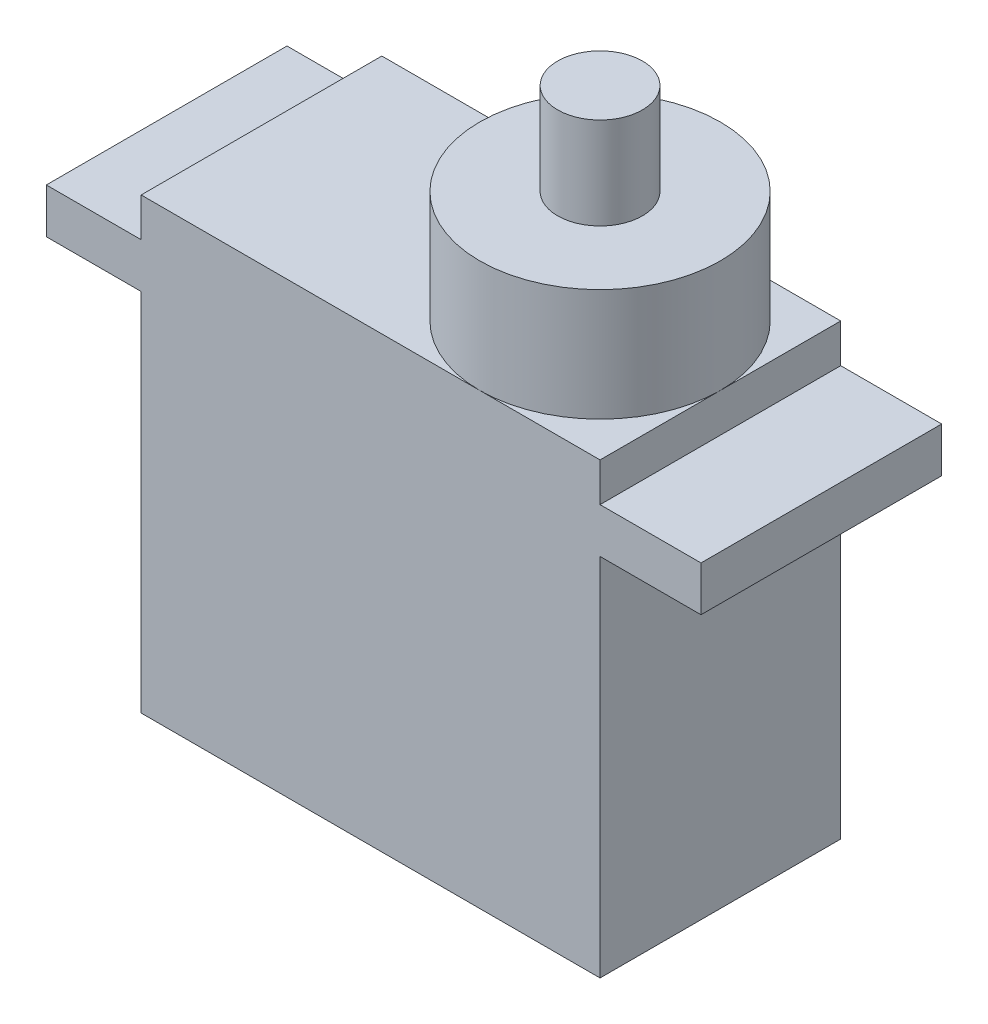
SolidWorks part; units mm, degrees
material "PF"
ref_plane "Front Plane" through (0, 0, 0) normal (0, 0, 1) x (1, 0, 0)
ref_plane "Top Plane" through (0, 0, 0) normal (0, 1, 0) x (1, 0, 0)
ref_plane "Right Plane" through (0, 0, 0) normal (1, 0, 0) x (0, 0, -1)
sketch "Sketch1" plane through (0, 0, 0) normal (0, 1, 0) x (1, 0, 0)
  line L1 (22.5, 11.8) -> (0, 11.8)
  line L2 (22.5, 11.8) -> (22.5, 0)
  line L3 (22.5, 0) -> (0, 0)
  line L4 (0, 11.8) -> (0, 0)
  point P5 (0, 0)
  dimension "D1" = 22.5
  dimension "D2" = 11.8
extrude "Boss-Extrude1" add sketch "Sketch1" along normal blind 17.9
ref_plane "Plane1" through (0, 17.9, 0) normal (0, 1, 0) x (1, 0, 0)
sketch "Sketch2" plane through (0, 17.9, 0) normal (0, 1, 0) x (1, 0, 0)
  line L4 (22.5, 0) -> (22.5, 11.8)
  line L5 (22.5, 11.8) -> (0, 11.8)
  line L6 (0, 11.8) -> (0, 0)
  line L7 (0, 0) -> (22.5, 0)
  line L8 (22.5, 0) -> (22.5, 11.8)
  line L9 (22.5, 11.8) -> (0, 11.8)
  line L10 (0, 11.8) -> (0, 0)
  line L11 (0, 0) -> (22.5, 0)
  dimension "D1" = 0
extrude "Boss-Extrude2" add sketch "Sketch2" along normal blind 4.1
sketch "Sketch3" plane through (0, 22, 0) normal (0, 1, 0) x (1, 0, 0)
  line L4 (0, 0) -> (22.5, 0)
  line L5 (22.5, 0) -> (22.5, 11.8)
  line L6 (22.5, 11.8) -> (0, 11.8)
  line L7 (0, 11.8) -> (0, 0)
  line L8 (0, 0) -> (22.5, 0)
  line L9 (22.5, 0) -> (22.5, 11.8)
  line L10 (22.5, 11.8) -> (0, 11.8)
  line L11 (0, 11.8) -> (0, 0)
  circle A0 centre (16.6, 5.9) radius 5.9
  point P4 (16.0443, 6.9455)
  dimension "D1" = 0
extrude "Boss-Extrude3" add sketch "Sketch3" along normal blind 5.5 contours A0
sketch "Sketch4" plane through (0, 27.5, 0) normal (0, 1, 0) x (1, 0, 0)
  circle A0 centre (16.6, 5.9) radius 2.0783
  circle A1 centre (16.6, 5.9) radius 5.9
  circle A2 centre (16.6, 5.9) radius 5.9
  dimension "D1" = 0
extrude "Boss-Extrude4" add sketch "Sketch4" along normal blind 4.5 contours A0
sketch "Sketch5" plane through (0, 17.9, 0) normal (0, 1, 0) x (1, 0, 0)
  line L0 (-4.65, 11.8) -> (-4.65, 0)
  line L1 (27.45, 11.8) -> (27.45, 0)
  line L2 (0, -6.49) -> (0, 6.49) construction
  line L4 (22.5, 0) -> (22.5, 11.8)
  line L5 (0, 0) -> (22.5, 0)
  line L6 (0, 11.8) -> (0, 0)
  line L7 (22.5, 11.8) -> (0, 11.8)
  line L9 (-4.65, 0) -> (27.45, 0)
  line L11 (27.45, 11.8) -> (-4.65, 11.8)
  point P3 (38.6321, 0)
  point P5 (-8.1362, 0)
  point P6 (0, 0)
  point P7 (-7.0709, 12.4)
  point P11 (0, 0)
  point P12 (38.2052, 0)
  point P13 (44.7974, 12.4)
  point P15 (45.1686, 12.4)
  dimension "D2" = 32.1
  dimension "D3" = 4.65
  dimension "D1" = 0
extrude "Boss-Extrude5" add sketch "Sketch5" along normal blind 2.2
